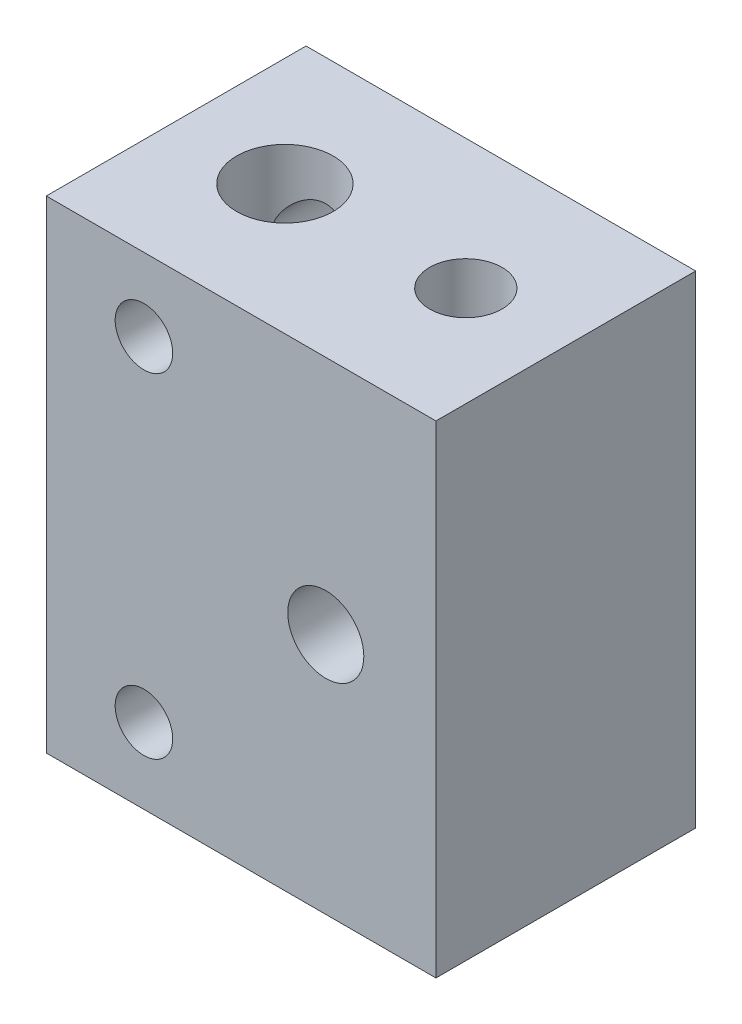
SolidWorks part; units mm, degrees
ref_plane "Front Plane" through (0, 0, 0) normal (0, 0, 1) x (1, 0, 0)
ref_plane "Top Plane" through (0, 0, 0) normal (0, 1, 0) x (1, 0, 0)
ref_plane "Right Plane" through (0, 0, 0) normal (1, 0, 0) x (0, 0, -1)
sketch "Sketch1" plane through (0, 0, 0) normal (0, 1, 0) x (1, 0, 0)
  line L0 (-186.0519, 0) -> (9116.5423, 0) construction
  line L1 (0, -186.0519) -> (0, 9116.5423) construction
  line L3 (10.5, -7) -> (10.5, 7)
  line L6 (-10.5, 7) -> (-10.5, -7)
  line L8 (-10.5, 7) -> (10.5, 7)
  line L9 (10.5, -7) -> (-10.5, -7)
  dimension "D1" = 21
  dimension "D2" = 14
  dimension "D3" = 7
  dimension "D4" = 10.5
extrude "Boss-Extrude2" add sketch "Sketch1" along normal blind 26
sketch "Sketch3" plane through (0, 0, 7) normal (0, 0, 1) x (1, 0, 0)
  line L0 (-21.4927, 13) -> (21.4927, 13) construction
  line L1 (0, 29.7077) -> (0, -3.7077) construction
  line L2 (-10.5, 0) -> (10.5, 0) construction
  arc A0 (-3.6871, 4.0653) -> (-6.7871, 4.0653) centre (-5.2371, 4.0653) ccw
  arc A1 (-6.7871, 4.0653) -> (-3.6871, 4.0653) centre (-5.2371, 4.0653) ccw
  arc A2 (6.6129, 13.0653) -> (2.5129, 13.0653) centre (4.5629, 13.0653) ccw
  arc A3 (2.5129, 13.0653) -> (6.6129, 13.0653) centre (4.5629, 13.0653) ccw
  arc A4 (-3.6871, 22.0653) -> (-6.7871, 22.0653) centre (-5.2371, 22.0653) ccw
  arc A5 (-6.7871, 22.0653) -> (-3.6871, 22.0653) centre (-5.2371, 22.0653) ccw
  point P3 (0, 13)
  point P7 (0, 13)
  point P9 (0, 0)
  dimension "D2" = 1.55
  dimension "D3" = 2.05
  dimension "D4" = 1.55
  dimension "D1" = 13
  dimension "D5" = 18
  dimension "D6" = 9.8
  dimension "D7" = 4.5629
  dimension "D8" = 5.2371
extrude "Cut-Extrude1" cut sketch "Sketch3" against normal blind 26
sketch "Sketch4" plane through (0, 26, 0) normal (0, 1, 0) x (1, 0, 0)
  line L0 (-14.955, 0) -> (14.955, 0) construction
  line L1 (0, 8.8937) -> (0, -8.8937) construction
  arc A0 (-2.0406, 0) -> (-7.2406, 0) centre (-4.6406, 0) ccw
  arc A1 (-7.2406, 0) -> (-2.0406, 0) centre (-4.6406, 0) ccw
  arc A2 (3.1594, 0) -> (7.0594, 0) centre (5.1094, 0) ccw
  arc A3 (7.0594, 0) -> (3.1594, 0) centre (5.1094, 0) ccw
  point P0 (0, 0)
  point P4 (0, 0)
  point P8 (0, 0)
  dimension "D1" = 2.6
  dimension "D2" = 1.95
  dimension "D3" = 1.95
extrude "Cut-Extrude2" cut sketch "Sketch4" against normal blind 26
